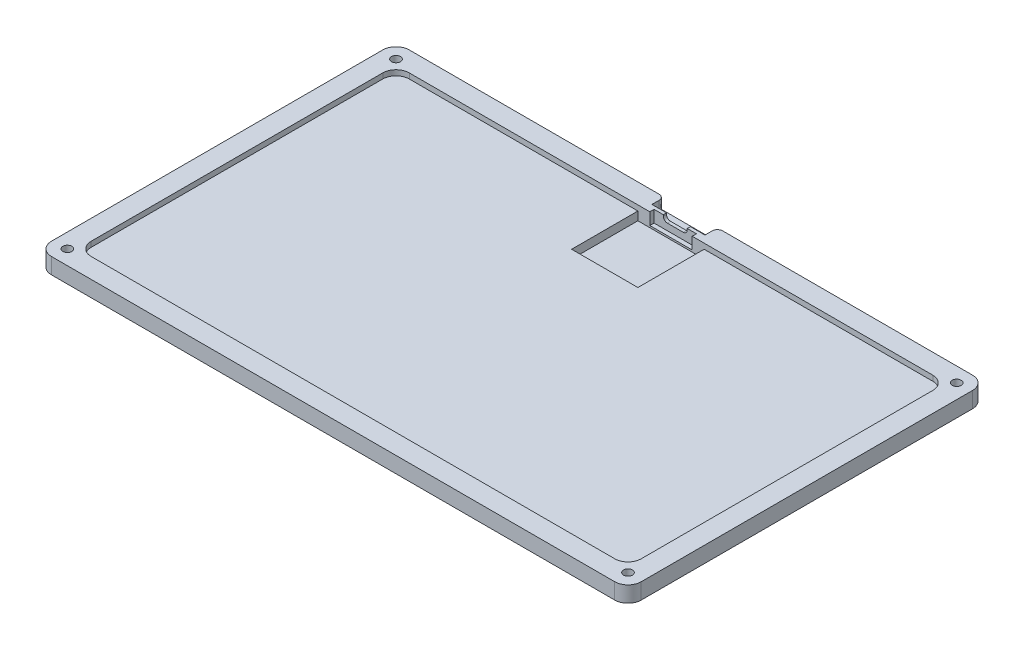
SolidWorks part; units mm, degrees
ref_plane "Front Plane" through (0, 0, 0) normal (0, 0, 1) x (1, 0, 0)
ref_plane "Top Plane" through (0, 0, 0) normal (0, 1, 0) x (1, 0, 0)
ref_plane "Right Plane" through (0, 0, 0) normal (1, 0, 0) x (0, 0, -1)
sketch "Sketch1" plane through (0, 0, 0) normal (0, 1, 0) x (1, 0, 0)
  line L0 (222.53, 130) -> (222.53, 5) construction
  line L1 (0, 0) -> (222.53, 0)
  line L2 (0, 0) -> (0, 135)
  line L3 (0, 135) -> (222.53, 135)
  line L4 (222.53, 0) -> (222.53, 135)
  line L5 (5, 135) -> (191.33, 135) construction
extrude "Boss-Extrude1" add sketch "Sketch1" along normal blind 6
fillet "Fillet1" radius 5 4 edges at (0, 3, -135) (0, 3, 0) (222.53, 3, -135) (222.53, 3, 0)
hole_wizard "CSK for M3 Flat Head Machine Screw1" positions "3DSketch2" profile "Sketch4" countersink size "M3" standard "ANSI Metric" end condition through all
sketch3d "3DSketch2"
  circle A4 centre (5.5, 19.2285, -5.5) radius 1.7 construction
  circle A5 centre (5.5, 19.2285, -129.5) radius 1.7 construction
  circle A6 centre (217.03, 19.2285, -5.5) radius 1.7 construction
  circle A7 centre (217.03, 19.2285, -129.5) radius 1.7 construction
  point P0 (5.5, 0, -129.5)
  point P2 (217.03, 0, -129.5)
  point P4 (217.03, 0, -5.5)
  point P6 (5.5, 0, -5.5)
  point P31 (5.5, 17.5285, -5.5)
  point P34 (5.5, 17.5285, -129.5)
  point P37 (217.03, 17.5285, -5.5)
  point P40 (217.03, 17.5285, -129.5)
sketch "Sketch4" plane through (5.5, 0, -129.5) normal (1, 0, 0) x (0, 0, -1)
  line L0 (0, 0) -> (0, 6)
  line L1 (0, 6) -> (1.7, 6)
  line L2 (1.7, 6) -> (1.7, 2.95)
  line L3 (1.7, 2.95) -> (3.15, 1.5)
  line L4 (3.15, 1.5) -> (3.15, 0)
  line L6 (3.15, 0) -> (0, 0)
  line L7 (-1.7, 2.95) -> (-3.15, 1.5) construction
  line L11 (0, -6.35) -> (0, 107.95) construction
  dimension "Thru Hole Dia." = 3.4
  dimension "Thru Hole Depth" = 6
  dimension "C'Sink Dia." = 6.3
  dimension "C'Sink Angle" = 90
  dimension "Head Clearance" = 1.5
chamfer "Chamfer1" distance 0.5 angle 45 4 edges at (217.03, 0, -132.65) (217.03, 0, -8.65) (5.5, 0, -132.65) (5.5, 0, -8.65)
sketch "Sketch6" plane through (0, 6, 0) normal (0, 1, 0) x (1, 0, 0)
  line L0 (217.53, 135) -> (5, 135) construction
  line L1 (12.5, 7.5) -> (210.03, 7.5)
  line L2 (7.5, 12.5) -> (7.5, 122.5)
  line L3 (12.5, 127.5) -> (210.03, 127.5)
  line L4 (215.03, 12.5) -> (215.03, 122.5)
  line L5 (0, 130) -> (0, 5) construction
  line L6 (5, 0) -> (217.53, 0) construction
  line L7 (222.53, 5) -> (222.53, 130) construction
  arc A0 (7.5, 122.5) -> (12.5, 127.5) centre (12.5, 122.5) cw
  arc A1 (12.5, 7.5) -> (7.5, 12.5) centre (12.5, 12.5) cw
  arc A2 (210.03, 7.5) -> (215.03, 12.5) centre (210.03, 12.5) ccw
  arc A3 (210.03, 127.5) -> (215.03, 122.5) centre (210.03, 122.5) cw
  dimension "D1" = 5
  dimension "D2" = 7.5
  dimension "D3" = 7.5
  dimension "D4" = 7.5
  dimension "D5" = 7.5
extrude "PCB Cutout" cut sketch "Sketch6" against normal blind 2
sketch "Sketch8" plane through (0, 6, 0) normal (0, 1, 0) x (1, 0, 0)
  line L1 (101.265, 135) -> (121.265, 135)
  line L2 (101.265, 135) -> (101.265, 130.3)
  line L3 (101.265, 130.3) -> (121.265, 130.3)
  line L4 (121.265, 135) -> (121.265, 130.3)
  line L5 (119.265, 129.1) -> (103.265, 129.1)
  line L6 (119.265, 129.1) -> (119.265, 127.5)
  line L7 (119.265, 127.5) -> (103.265, 127.5)
  line L8 (103.265, 129.1) -> (103.265, 127.5)
extrude "Cable Relief" cut sketch "Sketch8" against normal blind 4.5
sketch "Sketch9" plane through (0, 4, 0) normal (0, 1, 0) x (1, 0, 0)
  line L0 (103.265, 127.5) -> (12.5, 127.5) construction
  line L1 (98.765, 127.5) -> (123.765, 127.5)
  line L2 (98.765, 127.5) -> (98.765, 102.5)
  line L3 (98.765, 102.5) -> (123.765, 102.5)
  line L4 (123.765, 127.5) -> (123.765, 102.5)
  line L5 (0, 121.4733) -> (222.53, 121.4733) construction
  line L6 (0, 130) -> (0, 5) construction
  line L7 (222.53, 5) -> (222.53, 130) construction
  point P12 (111.265, 121.4733)
  point P13 (111.265, 127.5)
  dimension "D1" = 25
  dimension "D2" = 25
extrude "Pi Cutout" cut sketch "Sketch9" against normal blind 3.2
sketch "Sketch7" plane through (0, 0, -135) normal (0, 0, -1) x (-1, 0, 0)
  line L1 (-114.265, 7.8) -> (-108.265, 7.8)
  line L2 (-115.765, 6.3) -> (-115.765, 5.5)
  line L3 (-114.265, 4) -> (-108.265, 4)
  line L4 (-106.765, 6.3) -> (-106.765, 5.5)
  arc A0 (-114.265, 7.8) -> (-115.765, 6.3) centre (-114.265, 6.3) ccw
  arc A1 (-115.765, 5.5) -> (-114.265, 4) centre (-114.265, 5.5) ccw
  arc A2 (-108.265, 4) -> (-106.765, 5.5) centre (-108.265, 5.5) ccw
  arc A3 (-108.265, 7.8) -> (-106.765, 6.3) centre (-108.265, 6.3) cw
  point P8 (-115.765, 7.8)
  point P13 (-106.765, 4)
  dimension "D1" = 1.5
extrude "USB C Cutout" cut sketch "Sketch7" against normal up to next
sketch "Sketch5" plane through (0, 0, 0) normal (0, -1, 0) x (1, 0, 0)
  line L0 (111.265, 0) -> (111.265, -135) construction
  line L1 (5, 0) -> (217.53, 0) construction
  line L2 (217.53, -135) -> (5, -135) construction
  line L4 (213.5655, -126.0355) -> (8.9645, -126.0355)
  line L5 (213.5655, -126.0355) -> (213.5655, -8.9645)
  line L6 (213.5655, -8.9645) -> (8.9645, -8.9645)
  line L7 (8.9645, -126.0355) -> (8.9645, -8.9645)
  line L8 (213.5655, -126.0355) -> (8.9645, -8.9645) construction
  line L9 (213.5655, -8.9645) -> (8.9645, -126.0355) construction
  line L10 (127.765, -126.0355) -> (94.765, -126.0355)
  line L11 (127.765, -126.0355) -> (127.765, -99.0355)
  line L12 (127.765, -99.0355) -> (94.765, -99.0355)
  line L13 (94.765, -126.0355) -> (94.765, -99.0355)
  arc A0 (210.03, -127.5) -> (215.03, -122.5) centre (210.03, -122.5) ccw construction
  point P6 (111.265, -67.5)
  point P15 (111.265, -99.0355)
  dimension "D1" = 27
  dimension "D2" = 33
extrude "Mouse Pad Cutout" cut sketch "Sketch5" against normal blind 1.8 contours L4 L13 L12 L11 L5 L6 L7
fillet "Fillet2" radius 2 2 edges at (101.265, 3.75, -135) (121.265, 3.75, -135)
